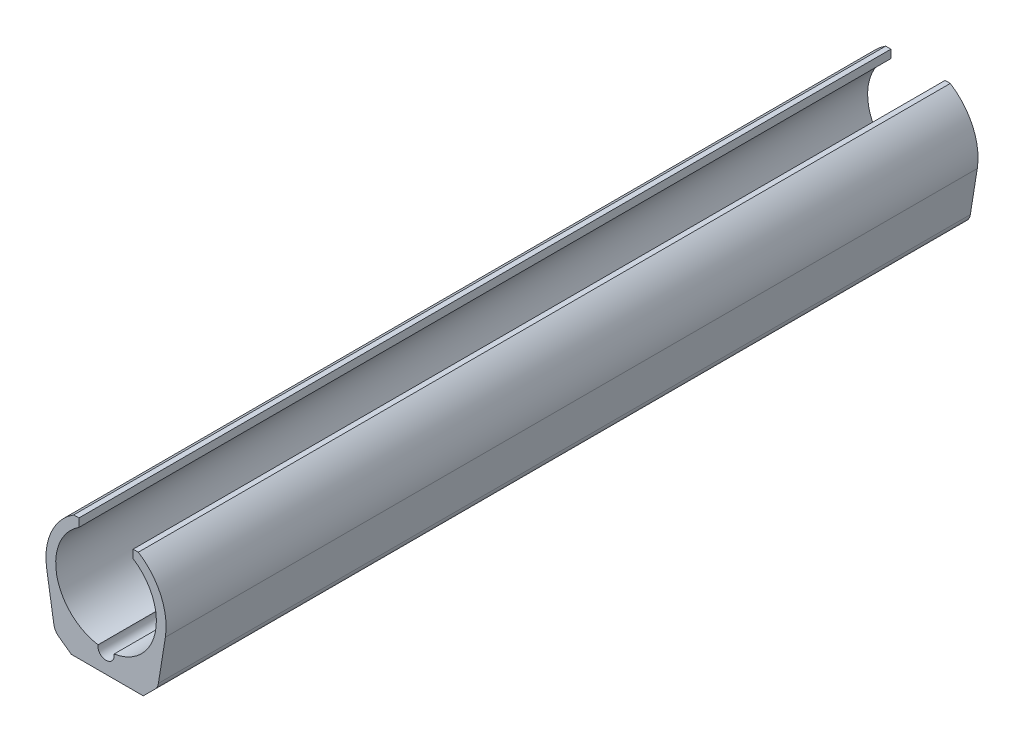
SolidWorks part; units mm, degrees
ref_plane "Plan de face" through (0, 0, 0) normal (0, 0, 1) x (1, 0, 0)
ref_plane "Plan de dessus" through (0, 0, 0) normal (0, 1, 0) x (1, 0, 0)
ref_plane "Plan de droite" through (0, 0, 0) normal (1, 0, 0) x (0, 0, -1)
sketch "Esquisse1" plane through (0, 0, 0) normal (0, 0, 1) x (1, 0, 0)
  line L1 (0, -16.306) -> (0, 16.306) construction
  line L3 (-12.1712, -17.5709) -> (12.1712, -17.5709)
  line L4 (-14.6133, -2.3436) -> (-12.1712, -17.5709)
  line L5 (14.6133, -2.3436) -> (12.1712, -17.5709)
  line L6 (-6.6695, 10.4536) -> (-6.6695, 12.4769)
  line L7 (-6.6695, 12.4769) -> (-7.9604, 12.4769)
  line L8 (6.6695, 12.4769) -> (7.9604, 12.4769)
  line L9 (6.6695, 10.4536) -> (6.6695, 12.4769)
  arc A0 (-7.9604, 12.4769) -> (-14.6133, -2.3436) centre (0, 0) ccw
  arc A1 (-6.6695, 10.4536) -> (-1.9728, -12.2421) centre (0, 0) ccw
  arc A2 (14.6133, -2.3436) -> (7.9604, 12.4769) centre (0, 0) ccw
  arc A3 (-1.9728, -12.2421) -> (1.9728, -12.2421) centre (0, -12.5709) ccw
  arc A4 (1.9728, -12.2421) -> (6.6695, 10.4536) centre (0, 0) ccw
  point P11 (0, -17.5709)
  dimension "D1" = 12.4
  dimension "D2" = 14.8
  dimension "D4" = 2
  dimension "D3" = 5
extrude "Boss.-Extru.1" add sketch "Esquisse1" along normal blind 200
chamfer "Chanfrein1" distance 3 angle 45 2 edges at (-12.1712, -17.5709, 100) (12.1712, -17.5709, 100)
fillet "Congé2" radius 3 2 edges at (12.7442, -13.9979, 100) (-12.6462, -14.6087, 100)
equation "\"rayon_int\"=12.4"
equation "\"D1@Esquisse1\"=\"rayon_int\""
equation "\"rayon_ext\"= \"rayon_int\" + 2.4"
equation "\"D2@Esquisse1\"=\"rayon_ext\""
